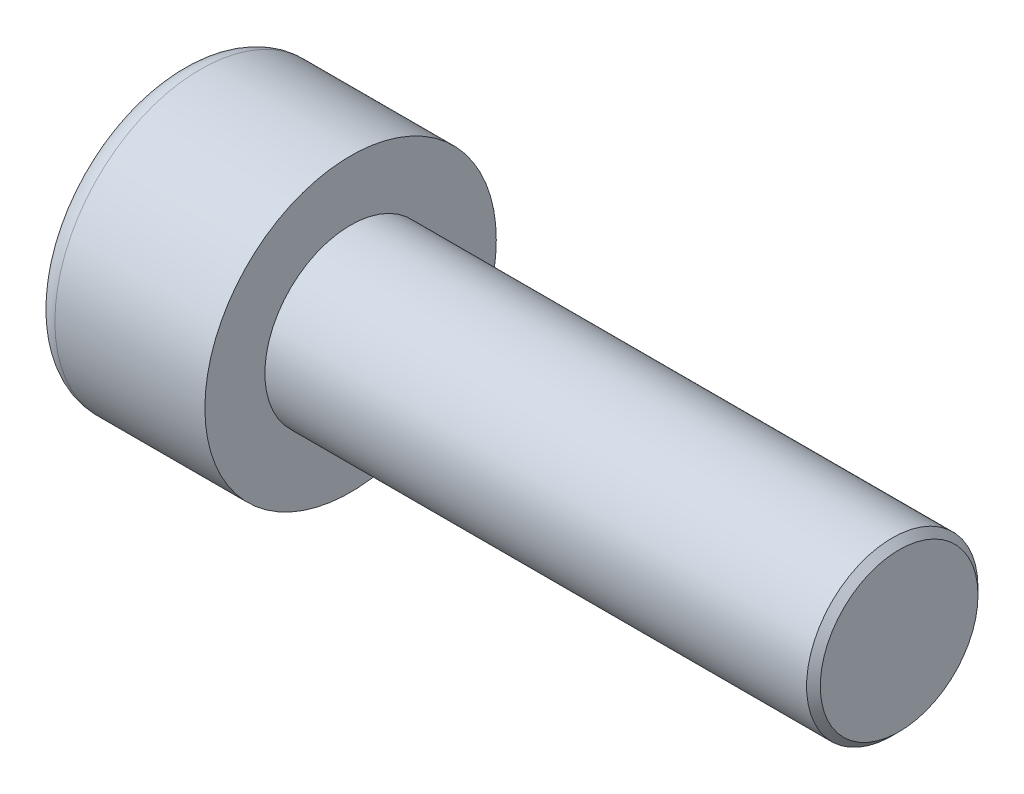
SolidWorks part; units mm, degrees
ref_plane "Front" through (0, 0, 0) normal (0, 0, 1) x (1, 0, 0)
ref_plane "Top" through (0, 0, 0) normal (0, 1, 0) x (1, 0, 0)
ref_plane "Right" through (0, 0, 0) normal (1, 0, 0) x (0, 0, -1)
sketch "Sketch1" plane through (0, 0, 0) normal (1, 0, 0) x (0, 0, -1)
  circle A0 centre (0, 0) radius 4.25
  dimension "dk" = 8.5
extrude "BaseHead" add sketch "Sketch1" along normal blind 5
sketch "Sketch2" plane through (5, 0, 0) normal (1, 0, 0) x (0, 0, -1)
  circle A0 centre (0, 0) radius 2.5
  dimension "d" = 5
extrude "BaseBody" add sketch "Sketch2" along normal blind 16
cosmetic thread "ThreadCosmetic1" parameters "b"=22, "D2"=4.134
sketch "Sketch3" plane through (0, 0, 0) normal (1, 0, 0) x (0, 0, -1)
  line L1 (2.3094, 0) -> (1.1547, 2)
  line L2 (1.1547, 2) -> (-1.1547, 2)
  line L3 (-1.1547, 2) -> (-2.3094, 0)
  line L4 (-2.3094, 0) -> (-1.1547, -2)
  line L5 (-1.1547, -2) -> (1.1547, -2)
  line L6 (1.1547, -2) -> (2.3094, 0)
  circle A0 centre (0, 0) radius 2 construction
  dimension "s" = 4
  dimension "e" = 4.6188
extrude "HexagonSocket" cut sketch "Sketch3" along normal blind 2.5
sketch "Sketch4" plane through (-4.1961, 0.75, 0) normal (0, 0, 1) x (-1, 0, 0)
  line L0 (-6.6961, 2.75) -> (-7.8508, 0.75)
  line L2 (-7.8508, 0.75) -> (-6.6961, 0.75)
  line L3 (-6.6961, 0.75) -> (-6.6961, 2.75)
  line L4 (-5.0351, 0.75) -> (0.839, 0.75) construction
  line L5 (-25.1961, 0.75) -> (-9.1961, 0.75) construction
  line L6 (-9.1961, 0.75) -> (-4.1961, 0.75) construction
  dimension "m" = 60
revolve "Cut-Revolve1" cut sketch "Sketch4" angle 360 about L4
fillet "HeadFillet" [suppressed] radius 0.2
fillet "TopFillet" radius 0.625 1 edges at (0, 0, -4.25)
chamfer "Chamfer1" distance 0.2 angle 45 1 edges at (21, 0, -2.5)
sketch "Sketch5" plane through (0, 0, 0) normal (0, 0, 1) x (1, 0, 0)
  line L0 (20.8, 2.125) -> (21.0165, 2.5)
  line L1 (21.0165, 2.5) -> (21.0165, 2.933)
  line L2 (21.0165, 2.933) -> (20.5835, 2.933)
  line L3 (20.5835, 2.933) -> (20.5835, 2.5)
  line L4 (20.5835, 2.5) -> (20.8, 2.125)
  line L5 (0, 0) -> (7.8886, 0) construction
  line L6 (20.8, -2.5) -> (20.8, 2.5) construction
  dimension "D1" = 5
  dimension "D2" = 0.433
revolve "Cut-Revolve10" [suppressed] cut sketch "Sketch5" angle 360 about L5
pattern_linear "LPattern10" [suppressed] count 42 spacing 0.5196 along (1, 0, 0)
equation "\"r1@TopFillet\" = \"d@Sketch2\" / 8"
equation "\"D1@Chamfer1\" = \"r@HeadFillet\""
equation "\"D1@Sketch5\" = \"d@Sketch2\""
equation "\"D2@Sketch5\" =  ( \"d@Sketch2\" - \"D2@ThreadCosmetic1\" )  / 2"
equation "\"D3@LPattern10\" = \"D2@Sketch5\" * 1.2"
equation "\"D1@LPattern10\" = \"b@ThreadCosmetic1\" / \"D3@LPattern10\""
